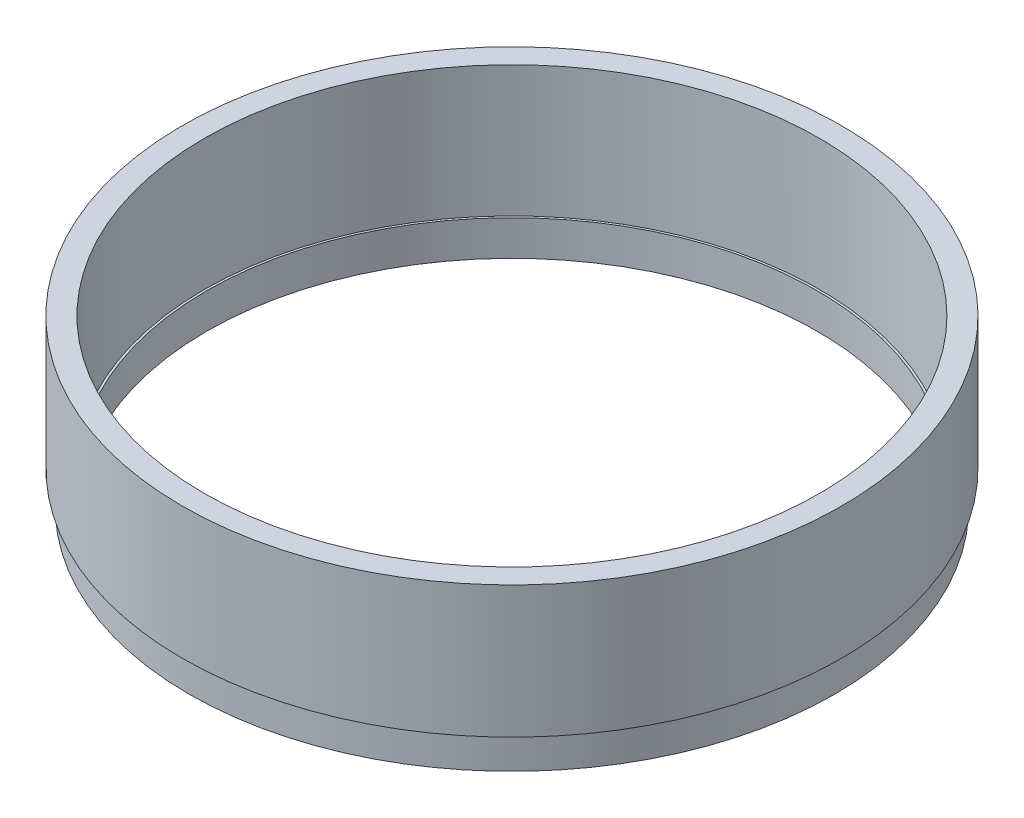
SolidWorks part; units mm, degrees
ref_plane "Alzado" through (0, 0, 0) normal (0, 0, 1) x (1, 0, 0)
ref_plane "Planta" through (0, 0, 0) normal (0, 1, 0) x (1, 0, 0)
ref_plane "Vista lateral" through (0, 0, 0) normal (1, 0, 0) x (0, 0, -1)
sketch "Croquis1" plane through (0, 0, 0) normal (0, 1, 0) x (1, 0, 0)
  circle A0 centre (13.5413, 6.6268) radius 35
  circle A1 centre (13.5413, 6.6268) radius 37.5
extrude "Saliente-Extruir1" add sketch "Croquis1" along normal blind 15
sketch "Croquis2" plane through (0, 0, 0) normal (0, -1, 0) x (-1, 0, 0)
  point P0 (-13.5413, 6.6268)
ref_plane "Plano1" through (0, 0, -6.6268) normal (0, 0, 1) x (1, 0, 0)
sketch "Croquis3" plane through (0, 0, -6.6268) normal (0, 0, 1) x (1, 0, 0)
  line L0 (-23.9587, 0) -> (-22.7087, 0) construction
  line L1 (-22.7087, 0) -> (-22.7087, 0.1) construction
  line L2 (-22.7087, 0) -> (-22.7087, -1) construction
  line L3 (-22.7087, 0.1) -> (-21.2087, 0.1) construction
  line L4 (-22.7087, 0.1) -> (-23.2087, 0.1) construction
  line L5 (-21.2087, 0.1) -> (-21.2087, -3.9) construction
  line L7 (-23.2087, 0.1) -> (-21.2087, 0.1)
  line L8 (-23.2087, 0.1) -> (-23.2087, -3.9)
  line L9 (-23.2087, -3.9) -> (-21.2087, -3.9)
  line L10 (-21.2087, 0.1) -> (-21.2087, -3.9)
  point P7 (-22.7087, -1)
ref_plane "Plano2" through (0, -1, 0) normal (0, -1, 0) x (-1, 0, 0)
sketch "Croquis4" plane through (0, -1, 0) normal (0, -1, 0) x (-1, 0, 0)
  circle A0 centre (-13.5413, 6.6268) radius 36.25
sweep "Barrer1" add profiles "Croquis3" path "Croquis4"
